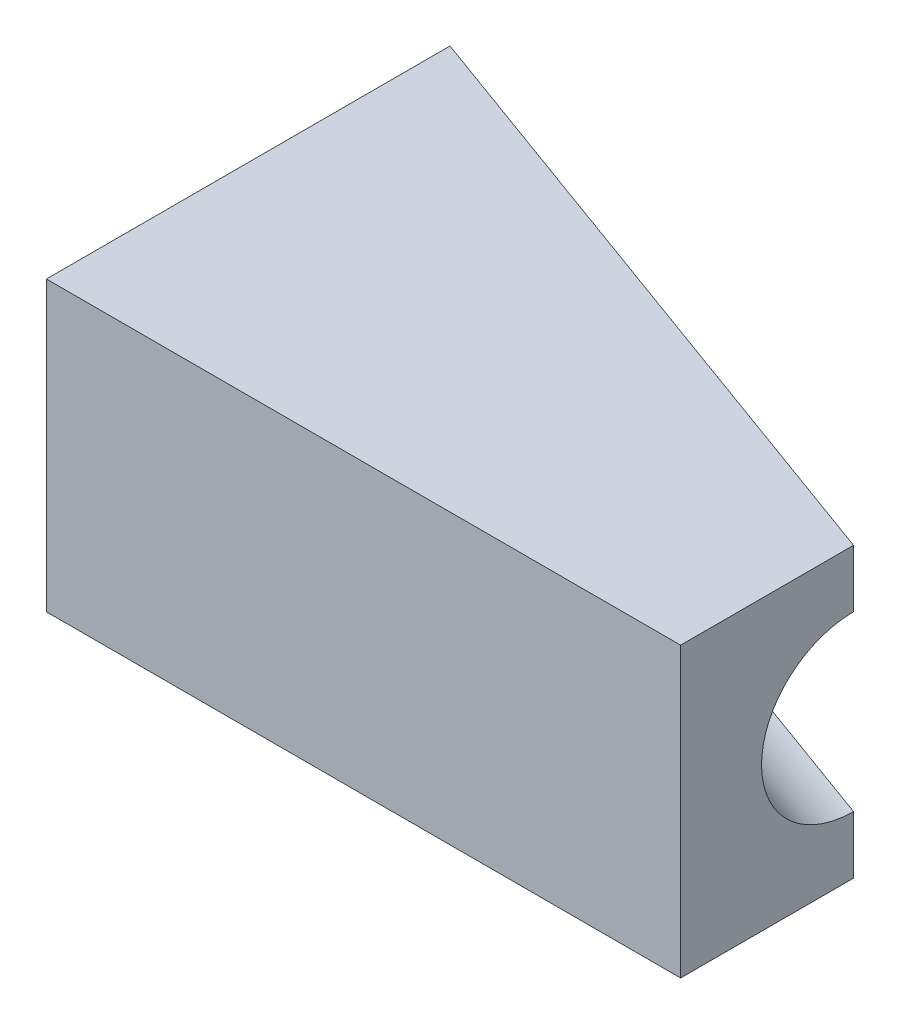
SolidWorks part; units mm, degrees
ref_plane "Front Plane" through (0, 0, 0) normal (0, 0, 1) x (1, 0, 0)
ref_plane "Top Plane" through (0, 0, 0) normal (0, 1, 0) x (1, 0, 0)
ref_plane "Right Plane" through (0, 0, 0) normal (1, 0, 0) x (0, 0, -1)
sketch "Sketch2" plane through (0, 0, 0) normal (0, 1, 0) x (1, 0, 0)
  line L0 (0, 0) -> (0, 40)
  line L1 (0, 40) -> (110, 0)
  line L2 (110, 0) -> (0, 0) construction
  line L3 (0, 0) -> (0, -30)
  line L4 (0, -30) -> (110, -30)
  line L5 (110, -30) -> (110, 0)
  dimension "D1" = 40
  dimension "D2" = 110
  dimension "D3" = 30
extrude "Boss-Extrude1" add sketch "Sketch2" along normal blind 50
ref_plane "Plane1" through (-12.8467, 0, -4.6715) normal (0.9398, 0, 0.3417) x (0.3417, 0, -0.9398)
sketch "Sketch3" plane through (-12.8467, 0, -4.6715) normal (0.9398, 0, 0.3417) x (0.3417, 0, -0.9398)
  line L2 (37.5917, 50) -> (37.5917, 0) construction
  circle A0 centre (37.5917, 25) radius 15
  point P4 (37.5917, 25)
  dimension "D1" = 30
extrude "Cut-Extrude2" cut sketch "Sketch3" along normal through all
